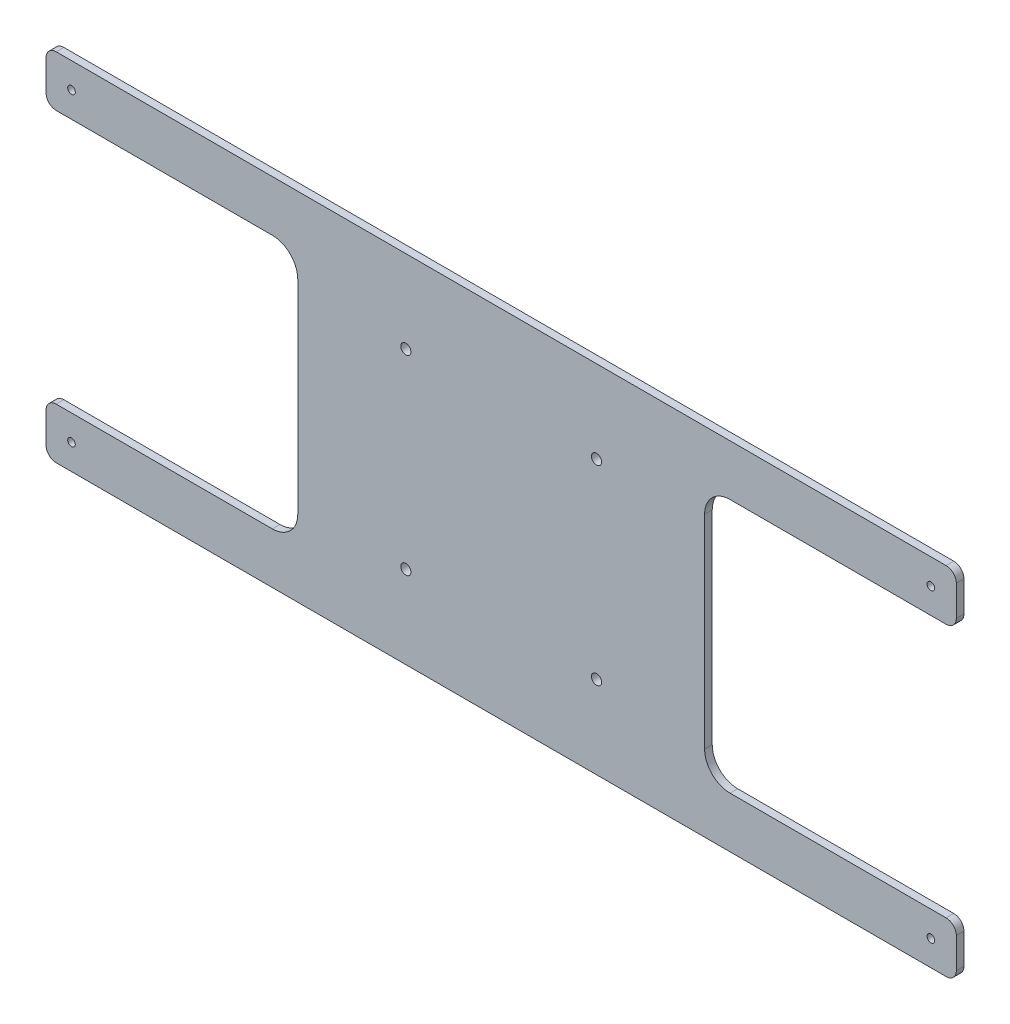
SolidWorks part; units mm, degrees
material "Polywood"
ref_plane "Front Plane" through (0, 0, 0) normal (0, 0, 1) x (1, 0, 0)
ref_plane "Top Plane" through (0, 0, 0) normal (0, 1, 0) x (1, 0, 0)
ref_plane "Right Plane" through (0, 0, 0) normal (1, 0, 0) x (0, 0, -1)
sketch "Sketch1" plane through (0, 0, 0) normal (0, 0, 1) x (1, 0, 0)
  line L0 (0, 0) -> (-115561.0944, 0) construction
  line L1 (0, 0) -> (0, 50000) construction
  line L2 (-164.5528, 70) -> (164.5528, 70)
  line L3 (-164.5528, 70) -> (-179, 70)
  line L4 (-179, 70) -> (-179, 50)
  line L5 (-179, 50) -> (-80, 50)
  line L6 (-80, 50) -> (-80, -50)
  line L7 (80, 50) -> (80, -50)
  line L8 (179, 50) -> (80, 50)
  line L9 (179, 70) -> (179, 50)
  line L10 (164.5528, 70) -> (179, 70)
  line L11 (164.5528, -70) -> (179, -70)
  line L12 (179, -70) -> (179, -50)
  line L13 (179, -50) -> (80, -50)
  line L14 (-179, -50) -> (-80, -50)
  line L15 (-179, -70) -> (-179, -50)
  line L16 (-164.5528, -70) -> (-179, -70)
  line L17 (-164.5528, -70) -> (164.5528, -70)
  circle A0 centre (-169, 60) radius 1.5
  circle A1 centre (-37.5, 37.5) radius 2
  circle A2 centre (37.5, 37.5) radius 2
  circle A3 centre (169, 60) radius 1.5
  circle A4 centre (169, -60) radius 1.5
  circle A5 centre (37.5, -37.5) radius 2
  circle A6 centre (-37.5, -37.5) radius 2
  circle A7 centre (-169, -60) radius 1.5
  point P24 (0, 70)
  point P36 (80, 0)
  point P37 (-80, 0)
  point P40 (0, -70)
  dimension "D2" = 3
  dimension "D9" = 4
  dimension "D1" = 60
  dimension "D3" = 169
  dimension "D4" = 37.5
  dimension "D5" = 10
  dimension "D6" = 20
  dimension "D7" = 10
  dimension "D8" = 80
  dimension "D10" = 37.5
extrude "Boss-Extrude1" add sketch "Sketch1" along normal blind 3
fillet "Fillet1" radius 4 8 edges at (179, -70, 1.5) (179, -50, 1.5) (179, 50, 1.5) (179, 70, 1.5) (-179, -70, 1.5) (-179, -50, 1.5) (-179, 50, 1.5) (-179, 70, 1.5)
fillet "Fillet2" radius 10 4 edges at (-80, 50, 1.5) (-80, -50, 1.5) (80, 50, 1.5) (80, -50, 1.5)
